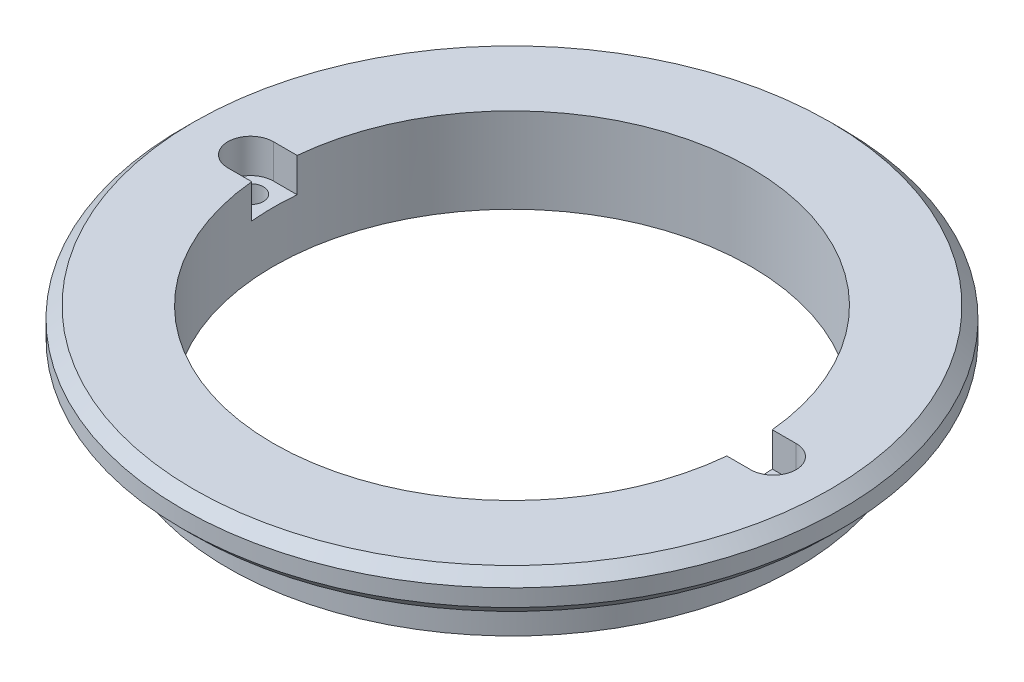
SolidWorks part; units mm, degrees
material "PLA"
ref_plane "Front Plane" through (0, 0, 0) normal (0, 0, 1) x (1, 0, 0)
ref_plane "Top Plane" through (0, 0, 0) normal (0, 1, 0) x (1, 0, 0)
ref_plane "Right Plane" through (0, 0, 0) normal (1, 0, 0) x (0, 0, -1)
sketch "Sketch1" plane through (0, 0, 0) normal (0, 0, 1) x (1, 0, 0)
  line L0 (0, 0) -> (0, 13.3216) construction
  line L1 (-29, 5) -> (-29, 6.5)
  line L2 (-28, 7.5) -> (-21, 7.5)
  line L3 (-21, 7.5) -> (-21, 0)
  line L4 (-21, 0) -> (-25, 0)
  line L5 (-28, 4) -> (-25, 4)
  line L6 (-25, 4) -> (-25, 0)
  line L7 (-29, 6.5) -> (-28, 7.5)
  line L8 (-29, 5) -> (-28, 4)
  point P4 (-29, 7.5)
  point P5 (-29, 4)
  dimension "D1" = 29
  dimension "D2" = 25
  dimension "D3" = 3.5
  dimension "D4" = 7.5
  dimension "D5" = 8
revolve "Revolve1" add sketch "Sketch1" angle 360 about L0
sketch "Sketch2" plane through (0, 0, 0) normal (0, -1, 0) x (1, 0, 0)
  circle A0 centre (0, 0) radius 23 construction
  circle A1 centre (0, 0) radius 25 construction
  circle A2 centre (-23, 0) radius 1.125
  circle A3 centre (23, 0) radius 1.125
  point P9 (0, 0)
  dimension "D1" = 2
  dimension "D2" = 2.25
  dimension "D3" = 2.25
extrude "Cut-Extrude1" cut sketch "Sketch2" against normal through all
sketch "Sketch3" plane through (0, 7.5, 0) normal (0, 1, 0) x (1, 0, 0)
  line L0 (-23, 2) -> (23, 2)
  line L1 (-23, -2) -> (23, -2)
  arc A0 (-23, 2) -> (-23, -2) centre (-23, 0) ccw
  arc A1 (23, -2) -> (23, 2) centre (23, 0) ccw
  point P10 (23, -2)
  point P11 (0, 0)
  point P12 (0, 0)
  point P13 (25.5574, -2)
  point P14 (0, 0)
  dimension "D2" = 4
extrude "Cut-Extrude3" cut sketch "Sketch3" against normal blind 3
